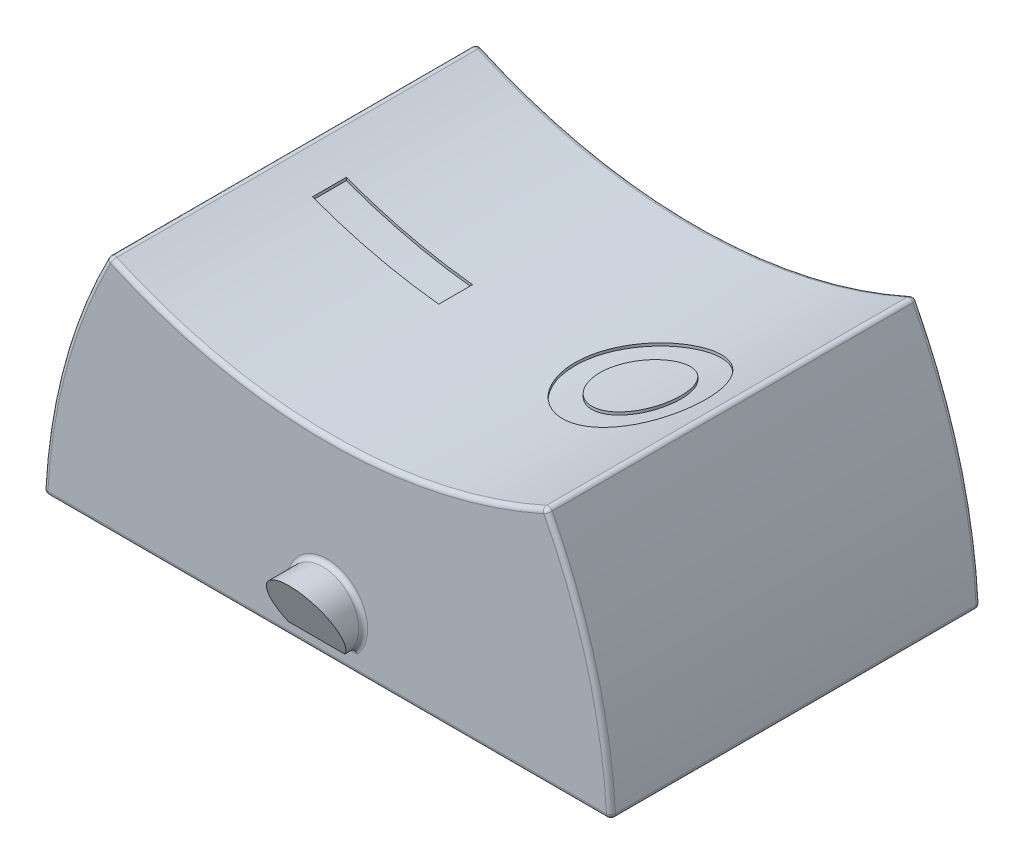
SolidWorks part; units mm, degrees
material "ABS"
ref_plane "Front Plane" through (0, 0, 0) normal (0, 0, 1) x (1, 0, 0)
ref_plane "Top Plane" through (0, 0, 0) normal (0, 1, 0) x (1, 0, 0)
ref_plane "Right Plane" through (0, 0, 0) normal (1, 0, 0) x (0, 0, -1)
sketch "Sketch1" plane through (0, 0, 0) normal (0, 0, -1) x (-1, 0, 0)
  line L0 (8.0065, -0.762) -> (-8.0065, -0.762) construction
  line L1 (-8.001, 0) -> (8.001, 0)
  line L2 (0, -0.762) -> (0, 0) construction
  line L3 (0, 0) -> (0, 5.3815) construction
  arc A1 (-6.1595, 6.731) -> (-8.001, 0) centre (8.0065, -0.762) ccw
  arc A2 (8.001, 0) -> (6.1595, 6.731) centre (-8.0065, -0.762) ccw
  arc A5 (6.1595, 6.731) -> (-6.1595, 6.731) centre (0, 20.1135) cw
  point P11 (0, 0)
  dimension "D4" = 14.732
  dimension "D1" = 16.002
  dimension "D3" = 6.731
  dimension "D5" = 12.319
  dimension "D6" = 0.762
extrude "Boss-Extrude1" add sketch "Sketch1" against normal mid plane 10.414
shell "Shell1" thickness 1.27
sketch "Sketch5" plane through (0, 0, 5.207) normal (0, 0, 1) x (1, 0, 0)
  line L0 (0.7931, 0.635) -> (-0.7931, 0.635)
  line L3 (8.001, 0) -> (-8.001, 0) construction
  arc A0 (-0.7931, 0.635) -> (0.7931, 0.635) centre (0, 1.27) cw
  dimension "D1" = 1.27
  dimension "D2" = 1.016
  dimension "D3" = 0.635
ref_plane "Plane1" through (0, -1.9944, 4.277) normal (0, -0.4226, 0.9063) x (1, 0, 0)
extrude "Boss-Extrude2" add sketch "Sketch5" along normal up to surface (0.2961 mm away) up to plane "Plane1"
mirror "Mirror2" about plane through (0, 0, 0) normal (0, 0, 1) of "Boss-Extrude2"
sketch "Sketch11" plane through (0, 0, 0) normal (0, -1, 0) x (1, 0, 0)
  line L0 (6.1595, 5.207) -> (6.1595, -5.207) construction
  line L1 (-1.5875, 0) -> (0, 0) construction
  line L2 (-5.1435, -0.4762) -> (-1.5875, -0.4762)
  line L3 (-5.1435, -0.4762) -> (-5.1435, 0.4762)
  line L4 (-5.1435, 0.4762) -> (-1.5875, 0.4763)
  line L5 (-1.5875, -0.4762) -> (-1.5875, 0.4763)
  line L6 (-6.1595, 5.207) -> (-6.1595, -5.207) construction
  circle A0 centre (3.6195, 0) radius 1.143
  circle A1 centre (3.6195, 0) radius 1.8415
  dimension "D1" = 3.683
  dimension "D2" = 2.286
  dimension "D3" = 2.54
  dimension "D4" = 3.556
  dimension "D5" = 1.016
  dimension "D6" = 0.9525
extrude "Cut-Extrude1" cut sketch "Sketch11" along normal offset from surface (19.3079 mm away) 0.0762 from offset 25.4 offset against normal yes
fillet "Fillet1" radius 0.127 28 edges at (-6.1595, 6.731, 0) (-8.001, 0, 0) (0, 0.635, -5.207) (0, 2.286, -5.207) (-7.4511, 3.467, -5.207) (0, 0, -5.207) (0, 5.3815, -5.207) (8.001, 0, 0) (6.1595, 6.731, 0) (7.4511, 3.467, -5.207) (0, 2.286, 5.207) (0, 0.635, 5.207) (7.4511, 3.467, 5.207) (0, 0, 5.207) (-7.4511, 3.467, 5.207) (0, 5.3815, 5.207) (0, 0, 3.937) (0, 0, -3.937) (-6.7294, 0, 0) (-6.3603, 2.6031, 3.937) (-6.3603, 2.6031, -3.937) (6.3603, 2.6031, 3.937) (6.7294, 0, 0) (6.3603, 2.6031, -3.937) (-5.535, 5.0993, 0) (0, 4.1115, 3.937) (5.535, 5.0993, 0) (0, 4.1115, -3.937)
